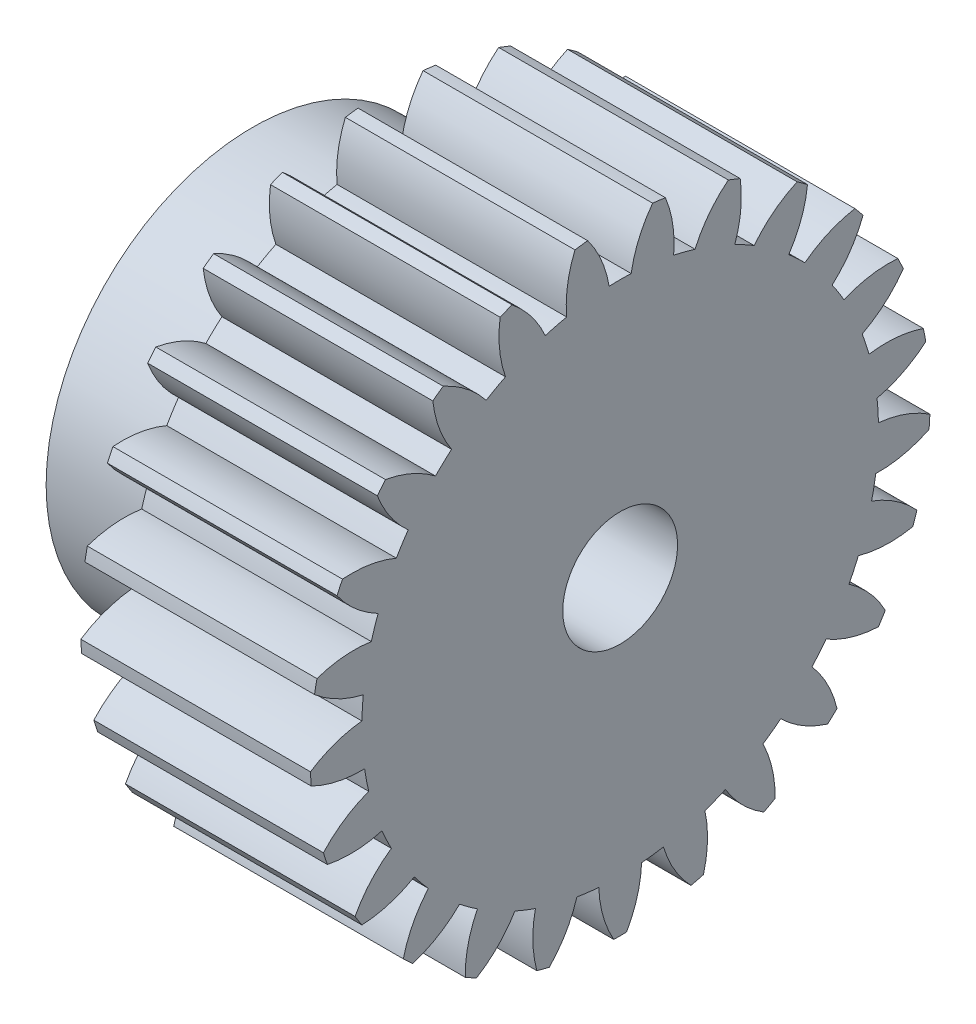
SolidWorks part; units mm, degrees
ref_plane "Plane1" through (0, 0, 0) normal (0, 0, 1) x (1, 0, 0)
ref_plane "Plane2" through (0, 0, 0) normal (0, 1, 0) x (1, 0, 0)
ref_plane "Plane3" through (0, 0, 0) normal (1, 0, 0) x (0, 0, -1)
sketch "HoldingSke" plane through (0, 0, 0) normal (0, 1, 0) x (1, 0, 0)
  line L0 (0, 0) -> (0.9063, -0.4226)
  line L1 (-15, 0) -> (100, 0) construction
  line L2 (0, 0) -> (-2.1039, 2.3779)
  line L3 (0, 0) -> (-11.863, 4.5341)
  line L4 (0, 0) -> (7.8269, 3.6497)
  line L5 (0, 0) -> (-14.9912, -5.5913)
  line L6 (0, 0) -> (-8.2896, -5.593)
  line L7 (-2.1039, 2.3779) -> (1.3401, 18.0029)
  line L8 (-76.2, 54.61) -> (-75.3, 54.61)
  line L9 (-71.009, 38.7566) -> (-53.1078, 45.2721)
  line L10 (-76.2, 71.12) -> (104.1128, 71.12)
  line L11 (0, 0) -> (-10, 0)
  line L12 (-76.2, 101.6) -> (-76.162, 101.6)
  line L13 (24.9733, 27.94) -> (52.9518, 28.4284)
  line L14 (24.9733, 27.94) -> (24.9743, 27.94)
  line L15 (24.9733, 27.94) -> (100.4006, 29.5858)
  line L16 (-63.627, -1) -> (-12.827, -1)
  circle A0 centre (0, 0) radius 2.5
  circle A1 centre (0, 0) radius 9
  circle A2 centre (0, 0) radius 9
  circle A3 centre (0, 0) radius 2.5
  dimension "MHD" = 18
  dimension "Hub_dia" = 18
  dimension "Bore" = 5
  dimension "MBD" = 5
  dimension "Num_teeth" = 25
  dimension "Pitch" = 1
  dimension "Overall_len" = 16
  dimension "Show_teeth" = 25
  dimension "Thickness" = 10
  dimension "OAL" = 16.0001
  dimension "T_dim" = 0.9
  dimension "Ap" = 20
  dimension "H" = 19.05
  dimension "Pitch_radius" = 180.3128
  dimension "Width" = 10
  dimension "Backlash" = 0.038
  dimension "Addendum_fac" = 1
  dimension "Dedendum_fac" = 1.25
  dimension "Clearance_fac" = 0.25
  dimension "Dedendum_add" = 0.001
  dimension "Module" = 1
sketch "BasProSke" plane through (0, 0, 0) normal (0, 1, 0) x (1, 0, 0)
  line L0 (-10, 0) -> (60, 0) construction
  line L1 (0, 0) -> (0, 13.5)
  line L2 (0, 0) -> (10, 0)
  line L3 (10, 0) -> (10, 13.5)
  line L4 (10, 13.5) -> (0, 13.5)
  dimension "Thickness" = 10
  dimension "Diameter" = 27
revolve "Base-Revolve" add sketch "BasProSke" angle 360 about L0
sketch "TooCutSke" plane through (0, 0, 0) normal (1, 0, 0) x (0, 0, -1)
  line L1 (0, 0) -> (0, 107) construction
  line L2 (0, 0) -> (-0.8514, 12.471) construction
  line L3 (0, 0) -> (-3.1282, 24.7619) construction
  line L4 (-0.8514, 12.471) -> (-1.5641, 12.3809) construction
  arc A0 (0.4801, 11.2388) -> (-0.4801, 11.2388) centre (0, 0) ccw
  arc A1 (1.4322, 13.4494) -> (-1.4322, 13.4494) centre (0, 0) ccw
  circle A2 centre (0, 0) radius 12.5 construction
  circle A3 centre (0, 0) radius 11.7462 construction
  arc A4 (-0.4801, 11.2388) -> (-1.4322, 13.4494) centre (-5.4133, 10.4244) ccw
  arc A5 (1.4322, 13.4494) -> (0.4801, 11.2388) centre (5.4133, 10.4244) ccw
  dimension "Root_dia" = 22.498
  dimension "Overcut_dia" = 27.0508
  dimension "Pitch_dia" = 25
  dimension "Base_dia" = 23.4923
  dimension "Flank_rad" = 5
  dimension "Half_ang" = 7.2
  dimension "Half_CT" = 0.7184
extrude "ToothCut" cut sketch "TooCutSke" along normal through all
fillet "Breaks" [suppressed] radius 0.02
fillet "RootFillets" [suppressed] radius 0.251
pattern_circular "TeethCuts" count 25 every 14.4 about axis through (-10, 0, 0) along (1, 0, 0) of "ToothCut", "RootFillets", "Breaks"
sketch "HubNeaOneSke" plane through (0, 0, 0) normal (-1, 0, 0) x (0, 0, 1)
  circle A0 centre (0, 0) radius 9
  dimension "Diameter" = 18
extrude "HubNearOne" add sketch "HubNeaOneSke" along normal blind 6.0001
sketch "HubNeaBotSke" plane through (0, 0, 0) normal (-1, 0, 0) x (0, 0, 1)
  circle A0 centre (0, 0) radius 9
  dimension "Diameter" = 18
extrude "HubNearBoth" [suppressed] add sketch "HubNeaBotSke" along normal blind 3
ref_plane "FarPln" through (10, 0, 0) normal (1, 0, 0) x (0, 0, -1)
sketch "HubFarSke" plane through (10, 0, 0) normal (1, 0, 0) x (0, 0, -1)
  circle A0 centre (0, 0) radius 9
  dimension "Diameter" = 18
extrude "HubFar" [suppressed] add sketch "HubFarSke" along normal blind 3
sketch "BorSke" plane through (0, 0, 0) normal (1, 0, 0) x (0, 0, -1)
  circle A0 centre (0, 0) radius 2.5
  dimension "Diameter" = 5
extrude "Bore" cut sketch "BorSke" along normal mid plane 32.0001
sketch "KeySke" plane through (0, 0, 0) normal (1, 0, 0) x (0, 0, -1)
  line L0 (-1, 0) -> (-1, 3.4)
  line L1 (-1, 3.4) -> (1, 3.4)
  line L2 (1, 3.4) -> (1, 0)
  line L3 (0, 0) -> (0, 34) construction
  line L4 (-1, 0) -> (1, 0)
  dimension "Offset" = 3.4
  dimension "Width" = 2
extrude "Keyway" [suppressed] cut sketch "KeySke" along normal mid plane 32.0001
pattern_circular "Keyway2" [suppressed] count 2 every 90 about axis through (-10, 0, 0) along (1, 0, 0)
equation "' \"Module@HoldingSke\" = 6.35"
equation "' \"Num_teeth@HoldingSke\" = 12"
equation "' \"Ap@HoldingSke\" =  20"
equation "' \"Ap@HoldingSke\" = 20"
equation "' \"Width@HoldingSke\" = 0.5 * 25.4"
equation "' \"Hub_dia@HoldingSke\"= 1 * 25.4"
equation "' \"Hub_dia@HoldingSke\" = 1 * 25.4"
equation "' \"Overall_len@HoldingSke\" = 1.0 * 25.4"
equation "' \"Bore@HoldingSke\" = 0.75 * 25.4"
equation "' \"T_dim@HoldingSke\" = 0.1 * 25.4"
equation "' \"Width@KeySke\" = 0.25 * 25.4"
equation "' \"Show_teeth@HoldingSke\" = 13"
equation "' \"Backlash@HoldingSke\" = 0.009 * 25.4"
equation "' \"Addendum_fac@HoldingSke\" = 1.0"
equation "' \"Dedendum_fac@HoldingSke\" = 1.25"
equation "' \"Dedendum_add@HoldingSke\" = 0.00005 * 25.4"
equation "' \"Clearance_fac@HoldingSke\" = 0.25"
equation "\"Pitch@HoldingSke\" = 1 / \"Module@HoldingSke\""
equation "\"Overcut_dia@TooCutSke\" = (\"Num_teeth@HoldingSke\" + 2 * \"Addendum_fac@HoldingSke\") / \"Pitch@HoldingSke\" + 0.002 * 25.4"
equation "\"Pitch_dia@TooCutSke\" = \"Num_teeth@HoldingSke\" / \"Pitch@HoldingSke\""
equation "\"Base_dia@TooCutSke\" = \"Num_teeth@HoldingSke\" / \"Pitch@HoldingSke\" * cos((\"Ap@HoldingSke\"  * 3.14159265 / 180))"
equation "\"Root_dia@TooCutSke\" = (\"Num_teeth@HoldingSke\" + 2) / \"Pitch@HoldingSke\" - 2 * (\"Addendum_fac@HoldingSke\" + \"Dedendum_fac@HoldingSke\") / \"Pitch@HoldingSke\" - \"Dedendum_add@HoldingSke\" * 2"
equation "\"Half_ang@TooCutSke\" = 180 / \"Num_teeth@HoldingSke\""
equation "\"Half_CT@TooCutSke\" = \"Num_teeth@HoldingSke\" / \"Pitch@HoldingSke\" * sin((3.14159265 / 2 / \"Num_teeth@HoldingSke\")) / 2 - 7 * \"Backlash@HoldingSke\" / 4"
equation "\"Flank_rad@TooCutSke\" = \"Num_teeth@HoldingSke\" / \"Pitch@HoldingSke\" / 5"
equation "\"Radius@RootFillets\" = \"Clearance_fac@HoldingSke\" / \"Pitch@HoldingSke\" + \"Dedendum_add@HoldingSke\""
equation "\"Break_rad@Breaks\" = 0.02 / \"Pitch@HoldingSke\""
equation "\"Thickness@HoldingSke\" = \"Width@HoldingSke\""
equation "\"OAL@HoldingSke\" = \"Thickness@HoldingSke\""
equation "\"MHD@HoldingSke\" = (\"Num_teeth@HoldingSke\" + 2) / \"Pitch@HoldingSke\" - 2 * (\"Addendum_fac@HoldingSke\" + \"Dedendum_fac@HoldingSke\")  / \"Pitch@HoldingSke\" - \"Dedendum_add@HoldingSke\" * 2"
equation "\"MBD@HoldingSke\" = (\"Num_teeth@HoldingSke\" + 2) / \"Pitch@HoldingSke\" - 2 * (\"Addendum_fac@HoldingSke\" + \"Dedendum_fac@HoldingSke\")  / \"Pitch@HoldingSke\" - \"Dedendum_add@HoldingSke\" * 2 - 0.002 * 25.4"
equation "\"MHD@HoldingSke\" = ((sgn( \"MHD@HoldingSke\" - \"Hub_dia@HoldingSke\" )-1)*( \"MHD@HoldingSke\" - \"Hub_dia@HoldingSke\" ))/-2+ \"Hub_dia@HoldingSke\""
equation "\"MBD@HoldingSke\" = ((sgn( \"MBD@HoldingSke\" - \"Bore@HoldingSke\" )-1)*( \"MBD@HoldingSke\" - \"Bore@HoldingSke\" ))/-2+ \"Bore@HoldingSke\""
equation "\"OAL@HoldingSke\" = ((sgn( \"OAL@HoldingSke\" - \"Overall_len@HoldingSke\" )+1)*( \"OAL@HoldingSke\" - \"Overall_len@HoldingSke\" ))/2 + \"Overall_len@HoldingSke\" + 0.000002 * 25.4"
equation "\"Num_teeth@TeethCuts\" = int( \"Show_teeth@HoldingSke\" ) + 1"
equation "\"Num_teeth@TeethCuts\" = ((sgn( \"Num_teeth@TeethCuts\" - \"Num_teeth@HoldingSke\" )-1)*( \"Num_teeth@TeethCuts\" - \"Num_teeth@HoldingSke\" ))/-2+ \"Num_teeth@HoldingSke\""
equation "\"Num_teeth@TeethCuts\" = ((sgn( \"Num_teeth@TeethCuts\" - 2.0)+1)*( \"Num_teeth@TeethCuts\" - 2.0))/2 +2.0"
equation "\"Angle@TeethCuts\" = 360.0 / \"Num_teeth@HoldingSke\""
equation "\"Diameter@BasProSke\" = (\"Num_teeth@HoldingSke\" + 2 * \"Addendum_fac@HoldingSke\") / \"Pitch@HoldingSke\""
equation "\"Thickness@BasProSke\"  = \"Thickness@HoldingSke\""
equation "' \"Fillet_rad@BasProSke\" =  \"Thickness@HoldingSke\" * 0.05"
equation "' \"Fillet_rad@BasProSke\" = \"Thickness@HoldingSke\" * 0.05"
equation "\"MHD@HoldingSke\" = ((sgn( \"MHD@HoldingSke\" - \"Root_dia@TooCutSke\" )-1)*( \"MHD@HoldingSke\" - \"Root_dia@TooCutSke\" ))/-2+ \"Root_dia@TooCutSke\""
equation "\"Diameter@HubNeaOneSke\" = \"MHD@HoldingSke\""
equation "\"Length@HubNearOne\" = \"OAL@HoldingSke\" - \"Thickness@BasProSke\""
equation "\"Diameter@HubNeaBotSke\" = \"MHD@HoldingSke\""
equation "\"Length@HubNearBoth\" = ( \"OAL@HoldingSke\" - \"Thickness@BasProSke\" ) / 2.0"
equation "\"Thickness@FarPln\" = \"Thickness@BasProSke\""
equation "\"Diameter@HubFarSke\" = \"MHD@HoldingSke\""
equation "\"Length@HubFar\" = ( \"OAL@HoldingSke\" - \"Thickness@BasProSke\" ) / 2.0"
equation "\"Diameter@BorSke\" = \"MBD@HoldingSke\""
equation "\"D1@Bore\" = \"OAL@HoldingSke\" * 2.0"
equation "\"D1@Keyway\" = \"OAL@HoldingSke\" * 2.0"
equation "\"Offset@KeySke\" = \"T_dim@HoldingSke\" + \"MBD@HoldingSke\" / 2.0"
